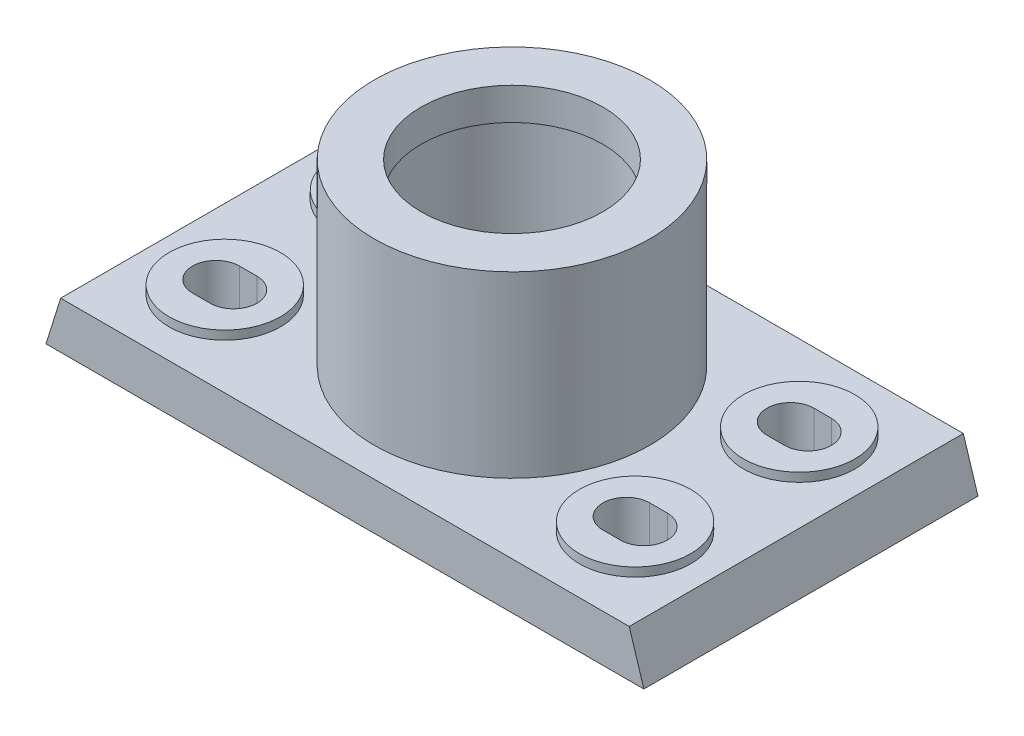
SolidWorks part; units mm, degrees
ref_plane "Front Plane" through (0, 0, 0) normal (0, 0, 1) x (1, 0, 0)
ref_plane "Top Plane" through (0, 0, 0) normal (0, 1, 0) x (1, 0, 0)
ref_plane "Right Plane" through (0, 0, 0) normal (1, 0, 0) x (0, 0, -1)
sketch "Sketch1" plane through (0, 0, 0) normal (0, 0, 1) x (1, 0, 0)
  line L0 (-102, 0) -> (102, 0)
  line L1 (-102, 0) -> (-97, 16)
  line L2 (0, 195.3499) -> (0, -75.2319) construction
  line L3 (-97, 16) -> (97, 16)
  line L4 (102, 0) -> (97, 16)
  line L5 (-145.7574, 16) -> (141.5074, 16) construction
  point P6 (0, 0)
  dimension "D1" = 16
  dimension "D2" = 5
  dimension "D3" = 16
  dimension "D4" = 5
  dimension "D5" = 204
extrude "Boss-Extrude1" add sketch "Sketch1" along normal mid plane 114
sketch "Sketch2" plane through (0, 0, 0) normal (0, -1, 0) x (1, 0, 0)
  line L0 (-102, -57) -> (102, -57) construction
  line L1 (-92, 47) -> (-6.5, 47)
  line L2 (-92, 47) -> (-92, -47)
  line L3 (-92, -47) -> (-6.5, -47)
  line L4 (-6.5, 47) -> (-6.5, -47)
  line L5 (-102, 57) -> (-102, -57) construction
  dimension "D1" = 85.5
  dimension "D2" = 94
  dimension "D3" = 10
  dimension "D4" = 10
extrude "Cut-Extrude1" cut sketch "Sketch2" against normal blind 3
mirror "Mirror1" about plane through (0, 0, 0) normal (1, 0, 0) of "Cut-Extrude1"
sketch "Sketch4" plane through (0, 16, 0) normal (0, 1, 0) x (1, 0, 0)
  circle A0 centre (0, 0) radius 47
  dimension "D1" = 94
extrude "Boss-Extrude2" add sketch "Sketch4" along normal blind 61
sketch "Sketch6" plane through (0, 16, 0) normal (0, 1, 0) x (1, 0, 0)
  line L0 (97, -57) -> (-97, -57) construction
  circle A0 centre (70, -28) radius 19
  circle A1 centre (70, 28) radius 19
  dimension "D1" = 29
  dimension "D3" = 56
  dimension "D4" = 38
  dimension "D2" = 70
extrude "Boss-Extrude4" add sketch "Sketch6" along normal blind 3
sketch "Sketch9" plane through (0, 19, 0) normal (0, 1, 0) x (1, 0, 0)
  line L0 (73, -28) -> (67, -28) construction
  line L1 (73, -36) -> (67, -36)
  line L2 (73, -20) -> (67, -20)
  arc A0 (73, -36) -> (73, -20) centre (73, -28) ccw
  arc A1 (67, -20) -> (67, -36) centre (67, -28) ccw
  point P2 (70, -28)
  dimension "D3" = 22
  dimension "D1" = 70
  dimension "D2" = 16
  dimension "D4" = 28
extrude "Cut-Extrude2" cut sketch "Sketch9" against normal through all
mirror "Mirror2" about plane through (0, 0, 0) normal (1, 0, 0) of "Boss-Extrude4"
mirror "Mirror3" about plane through (0, 0, 0) normal (0, 0, 1) of "Cut-Extrude2"
mirror "Mirror4" about plane through (0, 0, 0) normal (1, 0, 0) of "Mirror3", "Cut-Extrude2"
sketch "Sketch10" plane through (0, 77, 0) normal (0, 1, 0) x (1, 0, 0)
  circle A0 centre (0, 0) radius 31
  dimension "D1" = 62
extrude "Cut-Extrude3" cut sketch "Sketch10" against normal blind 11
sketch "Sketch11" plane through (0, 66, 0) normal (0, 1, 0) x (1, 0, 0)
  circle A0 centre (0, 0) radius 32.5
  dimension "D1" = 65
extrude "Cut-Extrude4" cut sketch "Sketch11" against normal blind 37
sketch "Sketch12" plane through (0, 29, 0) normal (0, 1, 0) x (1, 0, 0)
  circle A0 centre (0, 0) radius 31
  dimension "D1" = 62
extrude "Cut-Extrude5" cut sketch "Sketch12" against normal blind 13
sketch "Sketch13" plane through (0, 16, 0) normal (0, 1, 0) x (1, 0, 0)
  circle A0 centre (22, 0) radius 1.5
  dimension "D1" = 22
  dimension "D2" = 3
extrude "Cut-Extrude6" cut sketch "Sketch13" against normal blind 5
